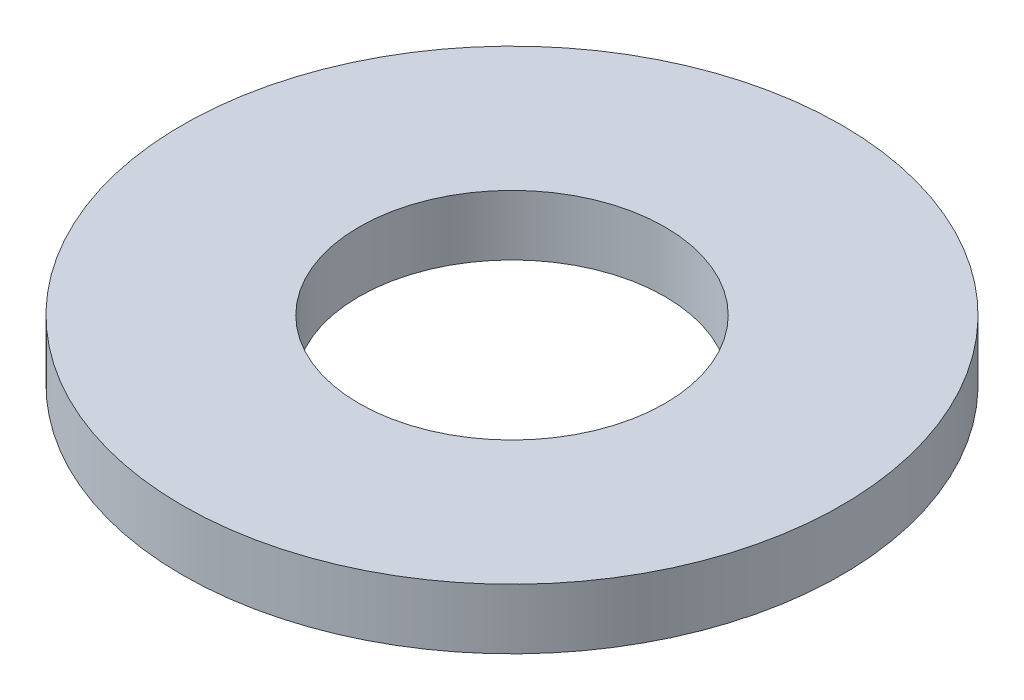
SolidWorks part; units mm, degrees
material "Plain Carbon Steel"
ref_plane "Front Plane" through (0, 0, 0) normal (0, 0, 1) x (1, 0, 0)
ref_plane "Top Plane" through (0, 0, 0) normal (0, 1, 0) x (1, 0, 0)
ref_plane "Right Plane" through (0, 0, 0) normal (1, 0, 0) x (0, 0, -1)
sketch "Sketch1" plane through (0, 0, 0) normal (0, 1, 0) x (1, 0, 0)
  circle A0 centre (0, 0) radius 5.5562
  dimension "OD" = 11.1125
extrude "Boss-Extrude1" add sketch "Sketch1" along normal blind 1.016
sketch "Sketch5" plane through (0, 1.016, 0) normal (0, 1, 0) x (-1, 0, 0)
  circle A0 centre (0, 0) radius 2.5781
  dimension "ID" = 5.1562
extrude "Cut-Extrude1" cut sketch "Sketch5" against normal through all
